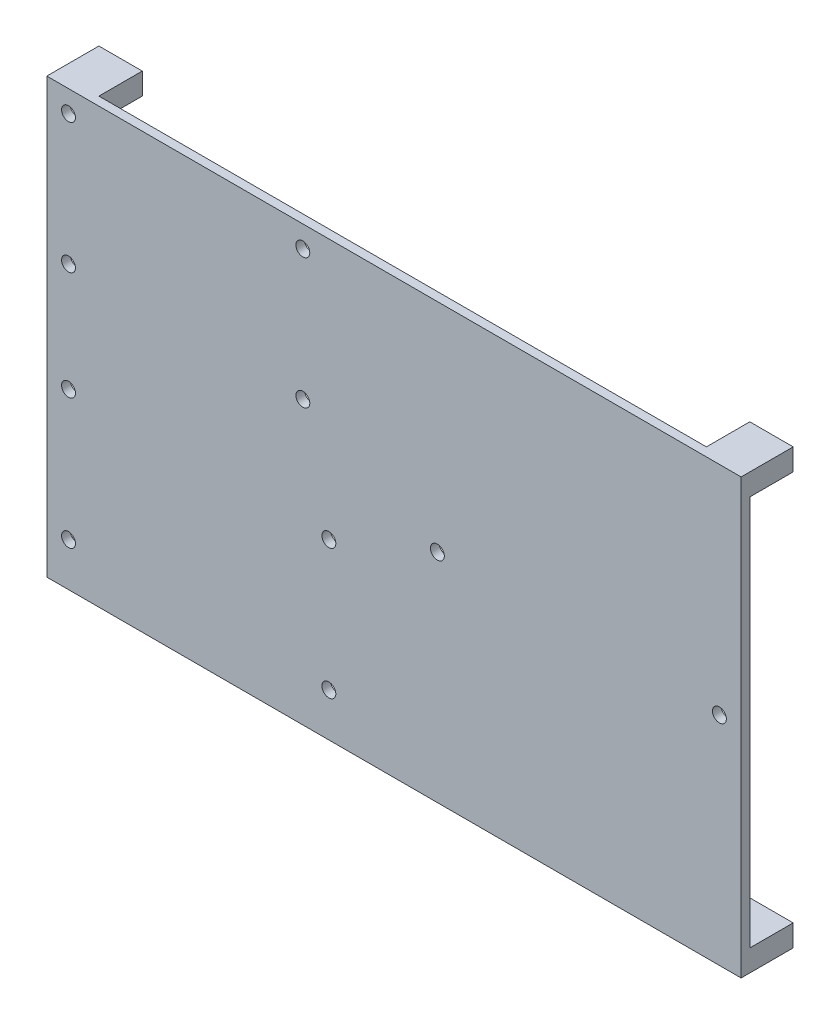
SolidWorks part; units mm, degrees
ref_plane "前视基准面" through (0, 0, 0) normal (0, 0, 1) x (1, 0, 0)
ref_plane "上视基准面" through (0, 0, 0) normal (0, 1, 0) x (1, 0, 0)
ref_plane "右视基准面" through (0, 0, 0) normal (1, 0, 0) x (0, 0, -1)
other "Configuration Table"
sketch "草图1" plane through (0, 0, 0) normal (0, 0, 1) x (1, 0, 0)
  line L0 (99.4662, -3.1379) -> (-60.5338, -3.1379) construction
  line L1 (-60.5338, 46.8621) -> (99.4662, 46.8621)
  line L2 (-60.5338, 46.8621) -> (-60.5338, -53.1379)
  line L3 (-60.5338, -53.1379) -> (99.4662, -53.1379)
  line L4 (99.4662, 46.8621) -> (99.4662, -53.1379)
  line L6 (29.4662, 29.2497) -> (94.4662, 29.2497) construction
  line L7 (29.4662, 29.2497) -> (29.4662, -33.8323) construction
  line L8 (29.4662, -33.8323) -> (94.4662, -33.8323) construction
  line L9 (94.4662, 29.2497) -> (94.4662, -33.8323) construction
  line L10 (-55.5338, -13.1379) -> (4.4662, -13.1379) construction
  line L11 (-55.5338, -13.1379) -> (-55.5338, -43.1379) construction
  line L12 (-55.5338, -43.1379) -> (4.4662, -43.1379) construction
  line L13 (4.4662, -13.1379) -> (4.4662, -43.1379) construction
  line L14 (-55.5338, 41.8621) -> (-1.5338, 41.8621) construction
  line L15 (-55.5338, 41.8621) -> (-55.5338, 11.8621) construction
  line L16 (-55.5338, 11.8621) -> (-1.5338, 11.8621) construction
  line L17 (-1.5338, 41.8621) -> (-1.5338, 11.8621) construction
  circle A0 centre (94.4662, -3.1379) radius 1.6
  circle A2 centre (29.4662, -3.1379) radius 1.6
  circle A3 centre (-55.5338, -43.1379) radius 1.6
  circle A4 centre (-55.5338, -13.1379) radius 1.6
  circle A5 centre (4.4662, -13.1379) radius 1.6
  circle A6 centre (4.4662, -43.1379) radius 1.6
  circle A7 centre (-55.5338, 41.8621) radius 1.6
  circle A8 centre (-55.5338, 11.8621) radius 1.6
  circle A9 centre (-1.5338, 11.8621) radius 1.6
  circle A10 centre (-1.5338, 41.8621) radius 1.6
  dimension "D5" = 3.2
  dimension "D8" = 3.2
  dimension "D11" = 3.2
  dimension "D1" = 160
  dimension "D2" = 100
  dimension "D3" = 65
  dimension "D4" = 5
  dimension "D6" = 60
  dimension "D7" = 30
  dimension "D9" = 30
  dimension "D10" = 54
  dimension "D12" = 5
  dimension "D13" = 15
  dimension "D14" = 10
extrude "凸台-拉伸1" add sketch "草图1" along normal blind 2
sketch "草图2" plane through (0, 0, 2) normal (0, 0, 1) x (1, 0, 0)
  line L0 (19.4662, 46.8621) -> (19.4662, -53.1379) construction
  line L1 (-60.5338, 46.8621) -> (-50.5338, 46.8621)
  line L2 (-60.5338, 46.8621) -> (-60.5338, 41.8621)
  line L3 (-60.5338, 41.8621) -> (-50.5338, 41.8621)
  line L4 (-50.5338, 46.8621) -> (-50.5338, 41.8621)
  line L5 (99.4662, 46.8621) -> (-60.5338, 46.8621) construction
  line L6 (-60.5338, -53.1379) -> (99.4662, -53.1379) construction
  line L7 (99.4662, 41.8621) -> (89.4662, 41.8621)
  line L8 (89.4662, 46.8621) -> (89.4662, 41.8621)
  line L9 (99.4662, 46.8621) -> (89.4662, 46.8621)
  line L10 (99.4662, 46.8621) -> (99.4662, 41.8621)
  line L11 (-60.5338, -3.1379) -> (99.4662, -3.1379) construction
  line L12 (-60.5338, 46.8621) -> (-60.5338, -53.1379) construction
  line L13 (99.4662, -53.1379) -> (99.4662, 46.8621) construction
  line L14 (99.4662, -53.1379) -> (99.4662, -48.1379)
  line L15 (99.4662, -53.1379) -> (89.4662, -53.1379)
  line L16 (89.4662, -53.1379) -> (89.4662, -48.1379)
  line L17 (99.4662, -48.1379) -> (89.4662, -48.1379)
  line L18 (-60.5338, -48.1379) -> (-50.5338, -48.1379)
  line L19 (-50.5338, -53.1379) -> (-50.5338, -48.1379)
  line L20 (-60.5338, -53.1379) -> (-50.5338, -53.1379)
  line L21 (-60.5338, -53.1379) -> (-60.5338, -48.1379)
  dimension "D1" = 10
  dimension "D2" = 5
extrude "凸台-拉伸2" add sketch "草图2" against normal blind 10 from surface at -2 starting at face at (19.4662, -3.1379, 0)
